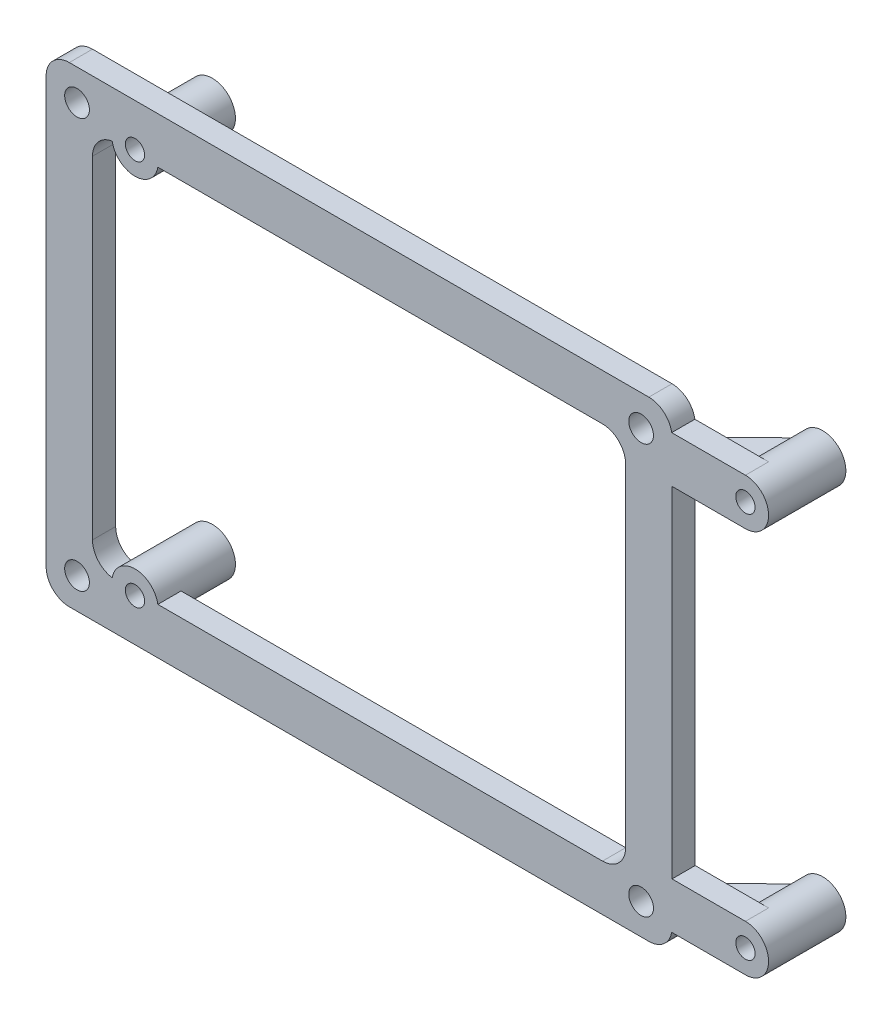
SolidWorks part; units mm, degrees
ref_plane "Front Plane" through (0, 0, 0) normal (0, 0, 1) x (1, 0, 0)
ref_plane "Top Plane" through (0, 0, 0) normal (0, 1, 0) x (1, 0, 0)
ref_plane "Right Plane" through (0, 0, 0) normal (1, 0, 0) x (0, 0, -1)
sketch "Sketch1" plane through (0, 0, 0) normal (0, 0, 1) x (1, 0, 0)
  line L1 (37.5, 27.5) -> (-37.5, 27.5)
  line L2 (37.5, 27.5) -> (37.5, -27.5)
  line L3 (37.5, -27.5) -> (-37.5, -27.5)
  line L4 (-37.5, 27.5) -> (-37.5, -27.5)
  line L5 (37.5, 27.5) -> (-37.5, -27.5) construction
  line L6 (37.5, -27.5) -> (-37.5, 27.5) construction
  point P0 (0, 0)
  dimension "D1" = 75
  dimension "D2" = 55
extrude "Extrude-Thin1" add sketch "Sketch1" along normal blind 3 thin thin type mid plane wall 6
sketch "Sketch2" plane through (0, 0, 3) normal (0, 0, 1) x (1, 0, 0)
  line L1 (36.5, 26.5) -> (-36.5, 26.5) construction
  line L2 (36.5, 26.5) -> (36.5, -26.5) construction
  line L3 (36.5, -26.5) -> (-36.5, -26.5) construction
  line L4 (-36.5, 26.5) -> (-36.5, -26.5) construction
  line L5 (36.5, 26.5) -> (-36.5, -26.5) construction
  line L6 (36.5, -26.5) -> (-36.5, 26.5) construction
  circle A0 centre (-36.5, 26.5) radius 1.6
  circle A1 centre (36.5, 26.5) radius 1.6
  circle A2 centre (36.5, -26.5) radius 1.6
  circle A3 centre (-36.5, -26.5) radius 1.6
  point P0 (0, 0)
  dimension "D3" = 3.2
  dimension "D1" = 73
  dimension "D2" = 53
extrude "Cut-Extrude1" cut sketch "Sketch2" against normal up to surface (3 mm away) up to face at (0, 0, 0)
fillet "Fillet1" radius 3 8 edges at (34.5, -24.5, 1.5) (34.5, 24.5, 1.5) (-34.5, -24.5, 1.5) (40.5, 30.5, 1.5) (40.5, -30.5, 1.5) (-40.5, -30.5, 1.5) (-40.5, 30.5, 1.5) (-34.5, 24.5, 1.5)
sketch "Sketch4" plane through (0, 0, 3) normal (0, 0, 1) x (1, 0, 0)
  line L0 (10.5, 0) -> (-41.6409, 0) construction
  line L2 (50, 25) -> (-29, 25) construction
  line L3 (50, 25) -> (50, -25) construction
  line L4 (50, -25) -> (-29, -25) construction
  line L5 (-29, 25) -> (-29, -25) construction
  line L6 (50, 25) -> (-29, -25) construction
  line L7 (50, -25) -> (-29, 25) construction
  line L8 (-34.5, 21.5) -> (-34.5, -21.5) construction
  line L9 (31.5, 24.5) -> (-31.5, 24.5) construction
  circle A0 centre (-29, 25) radius 3
  circle A1 centre (50, 25) radius 3
  circle A2 centre (50, -25) radius 3
  circle A3 centre (-29, -25) radius 3
  point P3 (10.5, 0)
  point P12 (0, 0)
  point P13 (0, 0)
  dimension "D3" = 6
  dimension "D1" = 79
  dimension "D2" = 50
  dimension "D4" = 5.5
  dimension "D5" = 0.5
extrude "Boss-Extrude1" add sketch "Sketch4" against normal blind 10
sketch "Sketch6" plane through (0, 0, 3) normal (0, 0, 1) x (1, 0, 0)
  line L0 (50, 28) -> (40.458, 28)
  line L1 (50, 22) -> (40.5, 22)
  line L2 (40.5, -27.5) -> (40.5, 27.5) construction
  line L3 (40.5, 22) -> (40.458, 28)
  line L4 (34.5, 0) -> (55.2158, 0) construction
  line L5 (34.5, -21.5) -> (34.5, 21.5) construction
  line L6 (40.5, -22) -> (40.458, -28)
  line L7 (50, -22) -> (40.5, -22)
  line L8 (50, -28) -> (40.458, -28)
  circle A0 centre (50, 25) radius 3 construction
  arc A1 (40.5, 27.5) -> (37.5, 30.5) centre (37.5, 27.5) ccw construction
  arc A2 (50, 28) -> (50, 22) centre (50, 25) cw
  arc A3 (50, -28) -> (50, -22) centre (50, -25) ccw
extrude "Boss-Extrude2" add sketch "Sketch6" against normal up to surface (3 mm away) up to face at (-34.9, -26.5, 0)
sketch "Sketch5" plane through (0, 0, -7) normal (0, 0, -1) x (-1, 0, 0)
  circle A0 centre (-50, 25) radius 1.25
  circle A1 centre (29, 25) radius 1.25
  circle A2 centre (-50, -25) radius 1.25
  circle A3 centre (29, -25) radius 1.25
  dimension "D1" = 2.5
extrude "Cut-Extrude2" cut sketch "Sketch5" against normal up to surface (10 mm away) up to face at (20.4706, 0, 3)
ref_plane "Plane1" through (0, 25, 0) normal (0, 1, 0) x (1, 0, 0)
sketch "Sketch7" plane through (0, 25, 0) normal (0, 1, 0) x (1, 0, 0)
  line L0 (47.6455, 7.001) -> (40.458, 0)
  point P4 (0, 0)
  point P5 (47.6455, 7.001)
rib "Rib2" sketch "Sketch7" sketch "Sketch7" thickness 2 extrusion direction parallel to sketch draft on no parameters "D1"=2
pattern_linear "LPattern1" count 2 spacing 50 along (0, -1, 0) of "Rib2"
